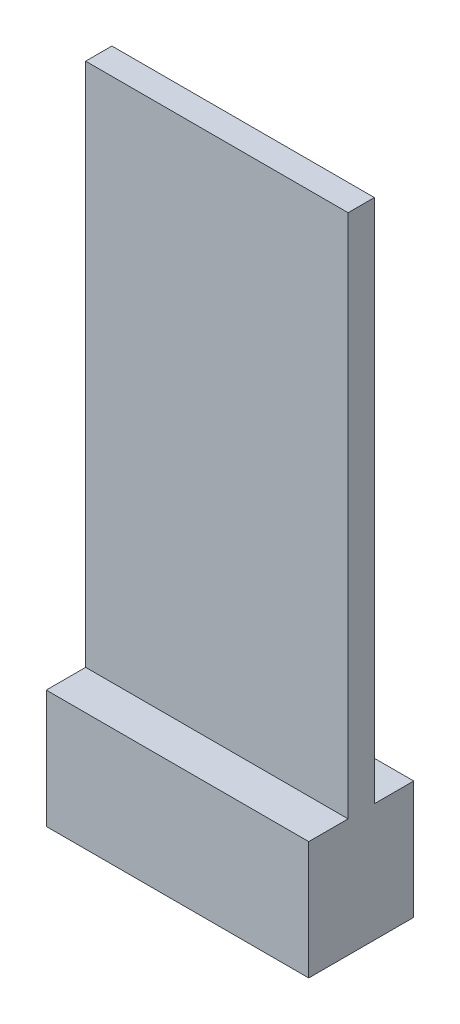
SolidWorks part; units mm, degrees
ref_plane "Front Plane" through (0, 0, 0) normal (0, 0, 1) x (1, 0, 0)
ref_plane "Top Plane" through (0, 0, 0) normal (0, 1, 0) x (1, 0, 0)
ref_plane "Right Plane" through (0, 0, 0) normal (1, 0, 0) x (0, 0, -1)
sketch "Sketch2" plane through (0, 0, 0) normal (0, 0, 1) x (1, 0, 0)
  line L1 (10, -4.5) -> (-10, -4.5)
  line L2 (10, -4.5) -> (10, 4.5)
  line L3 (10, 4.5) -> (-10, 4.5)
  line L4 (-10, -4.5) -> (-10, 4.5)
  line L5 (10, -4.5) -> (-10, 4.5) construction
  line L6 (10, 4.5) -> (-10, -4.5) construction
  point P0 (0, 0)
  dimension "D1" = 20
  dimension "D2" = 9
extrude "Boss-Extrude1" add sketch "Sketch2" along normal blind 8
sketch "Sketch3" plane through (-10, 0, 0) normal (-1, 0, 0) x (0, 0, 1)
  line L3 (2, -2.5) -> (6, -2.5)
  line L4 (2, -2.5) -> (2, 2.5)
  line L5 (2, 2.5) -> (6, 2.5)
  line L6 (6, -2.5) -> (6, 2.5)
  line L7 (2, -2.5) -> (6, 2.5) construction
  line L8 (2, 2.5) -> (6, -2.5) construction
  point P5 (4, 0)
  dimension "D1" = 4
  dimension "D2" = 5
extrude "Cut-Extrude1" cut sketch "Sketch3" against normal blind 10
sketch "Sketch6" plane through (0, 4.5, 0) normal (0, 1, 0) x (1, 0, 0)
  line L1 (10, -8) -> (10, 0) construction
  line L4 (-10, -3) -> (10, -3)
  line L5 (-10, -3) -> (-10, -5)
  line L6 (-10, -5) -> (10, -5)
  line L7 (10, -3) -> (10, -5)
  line L8 (-10, -3) -> (10, -5) construction
  line L9 (-10, -5) -> (10, -3) construction
  point P6 (0, -4)
  dimension "D1" = 2
extrude "Boss-Extrude3" add sketch "Sketch6" along normal blind 40
